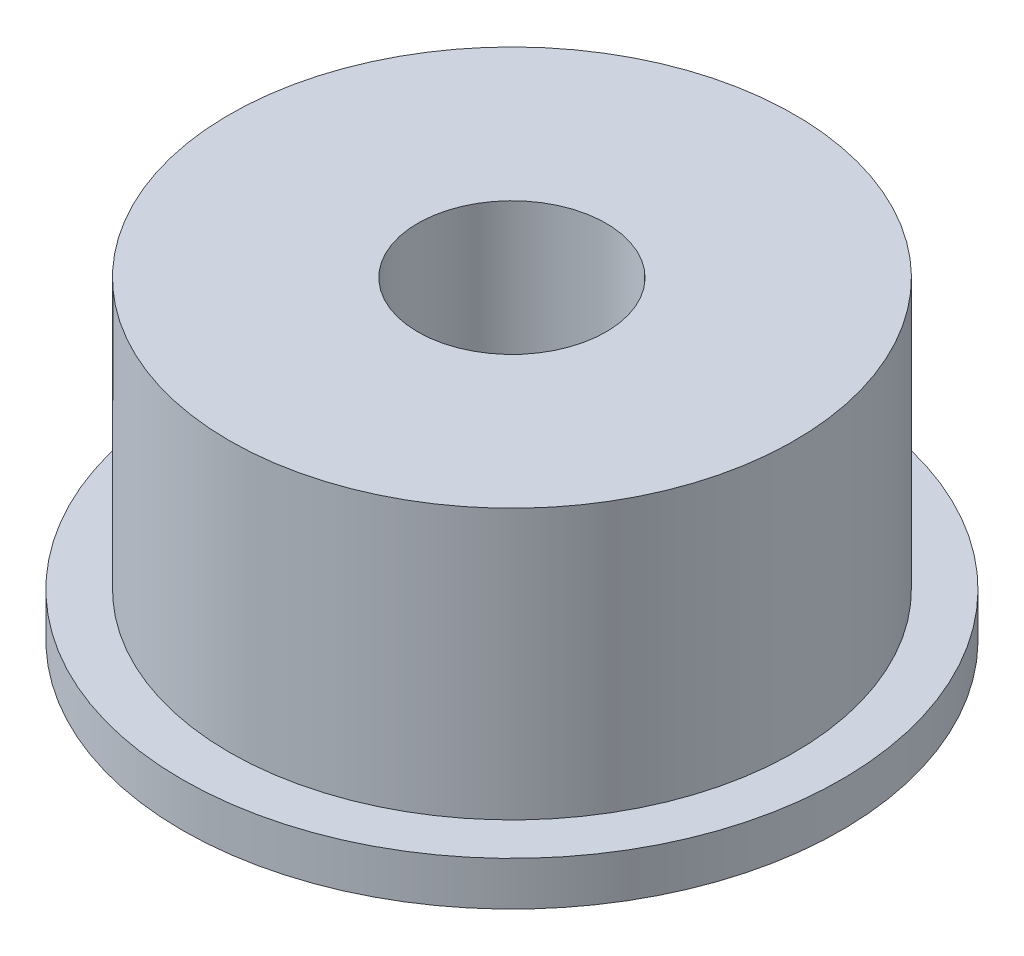
SolidWorks part; units mm, degrees
ref_plane "前视基准面" through (0, 0, 0) normal (0, 0, 1) x (1, 0, 0)
ref_plane "上视基准面" through (0, 0, 0) normal (0, 1, 0) x (1, 0, 0)
ref_plane "右视基准面" through (0, 0, 0) normal (1, 0, 0) x (0, 0, -1)
sketch "草图1" plane through (0, 0, 0) normal (0, 1, 0) x (1, 0, 0)
  circle A0 centre (0, 0) radius 5.25
  dimension "D1" = 10.5
extrude "凸台-拉伸1" add sketch "草图1" along normal blind 0.7
sketch "草图2" plane through (0, 0.7, 0) normal (0, 1, 0) x (1, 0, 0)
  circle A0 centre (0, 0) radius 4.5
  dimension "D1" = 9
extrude "凸台-拉伸2" add sketch "草图2" along normal blind 4.3
sketch "草图3" plane through (0, 5, 0) normal (0, 1, 0) x (1, 0, 0)
  circle A0 centre (0, 0) radius 1.5
  dimension "D1" = 3
extrude "切除-拉伸1" cut sketch "草图3" against normal through all
